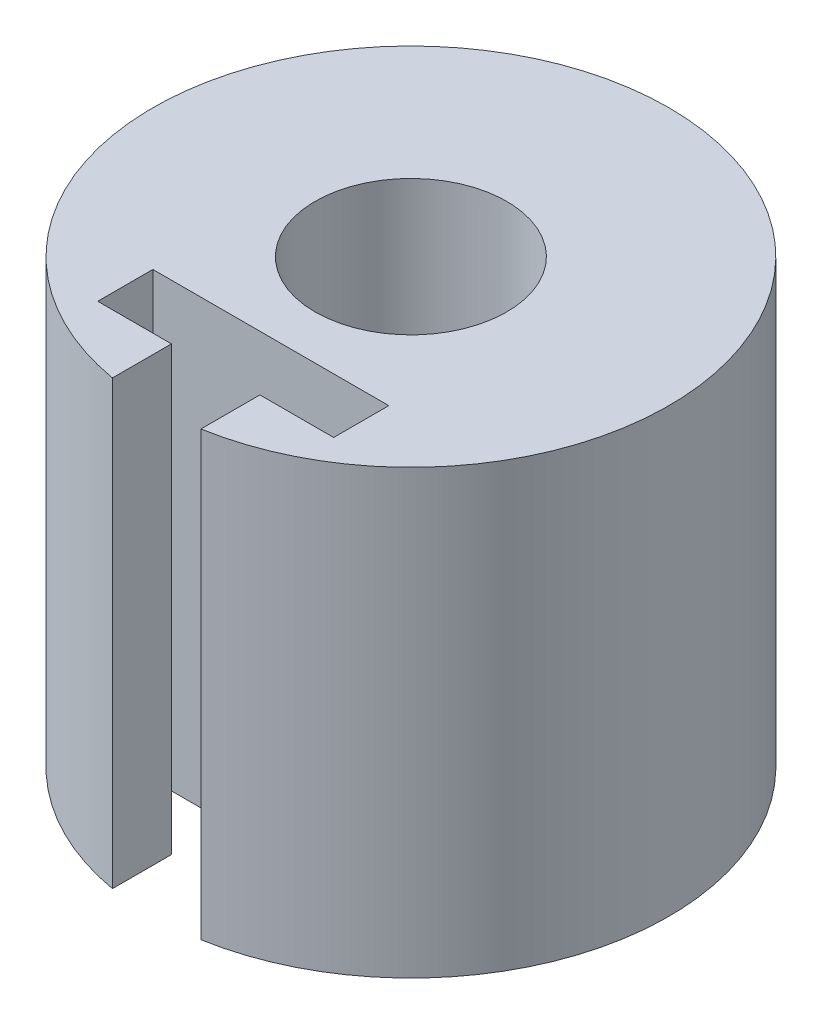
SolidWorks part; units mm, degrees
ref_plane "Front Plane" through (0, 0, 0) normal (0, 0, 1) x (1, 0, 0)
ref_plane "Top Plane" through (0, 0, 0) normal (0, 1, 0) x (1, 0, 0)
ref_plane "Right Plane" through (0, 0, 0) normal (1, 0, 0) x (0, 0, -1)
sketch "Sketch1" plane through (0, 0, 0) normal (0, 1, 0) x (1, 0, 0)
  circle A0 centre (0, 0) radius 3.25
  circle A1 centre (0, 0) radius 8.75
  dimension "D1" = 6.5
  dimension "D2" = 17.5
extrude "Boss-Extrude1" add sketch "Sketch1" along normal blind 15
ref_plane "Plane1" through (0, 0, 8.75) normal (0, 0, 1) x (1, 0, 0)
sketch "Sketch2" plane through (0, 0, 8.75) normal (0, 0, 1) x (1, 0, 0)
  line L1 (1.5, 0) -> (-1.5, 0)
  line L2 (1.5, 0) -> (1.5, 15)
  line L3 (1.5, 15) -> (-1.5, 15)
  line L4 (-1.5, 0) -> (-1.5, 15)
  line L5 (1.5, 0) -> (-1.5, 15) construction
  line L6 (1.5, 15) -> (-1.5, 0) construction
  line L8 (8.75, 15) -> (-8.75, 15) construction
  line L9 (-8.75, 0) -> (8.75, 0) construction
  point P0 (0, 7.5)
  point P9 (0, 0)
  dimension "D1" = 3
extrude "Cut-Extrude2" cut sketch "Sketch2" against normal blind 4
ref_plane "Plane2" through (0, 0, -8.75) normal (0, 0, -1) x (-1, 0, 0)
sketch "Sketch3" plane through (0, 0, -8.75) normal (0, 0, -1) x (-1, 0, 0)
  line L0 (-8.75, 15) -> (-8.75, 0) construction
  line L1 (-8.75, 15) -> (-8.75, 0) construction
  circle A0 centre (0, 7.5) radius 1.25
  point P2 (0, 0)
  point P6 (-8.75, 7.5)
  dimension "D1" = 2.5
extrude "Cut-Extrude3" cut sketch "Sketch3" against normal blind 8
ref_plane "Plane3" through (0, 0, 0) normal (-1, 0, 0) x (0, 0, 1)
sketch "Sketch5" plane through (0, 0, 0) normal (-1, 0, 0) x (0, 0, 1)
  line L0 (4.75, 15) -> (8.6205, 15) construction
  line L1 (6.6205, 0) -> (4.75, 0)
  line L2 (6.6205, 0) -> (6.6205, 15)
  line L3 (6.6205, 15) -> (4.75, 15)
  line L4 (4.75, 0) -> (4.75, 15)
  line L5 (6.6205, 0) -> (4.75, 15) construction
  line L6 (6.6205, 15) -> (4.75, 0) construction
  line L7 (4.75, 0) -> (8.6205, 0) construction
  line L8 (4.75, 0) -> (4.75, 15) construction
  line L9 (8.6205, 15) -> (8.6205, 0) construction
  point P0 (5.6852, 7.5)
  dimension "D1" = 2
extrude "Cut-Extrude4" cut sketch "Sketch5" against normal mid plane 8
